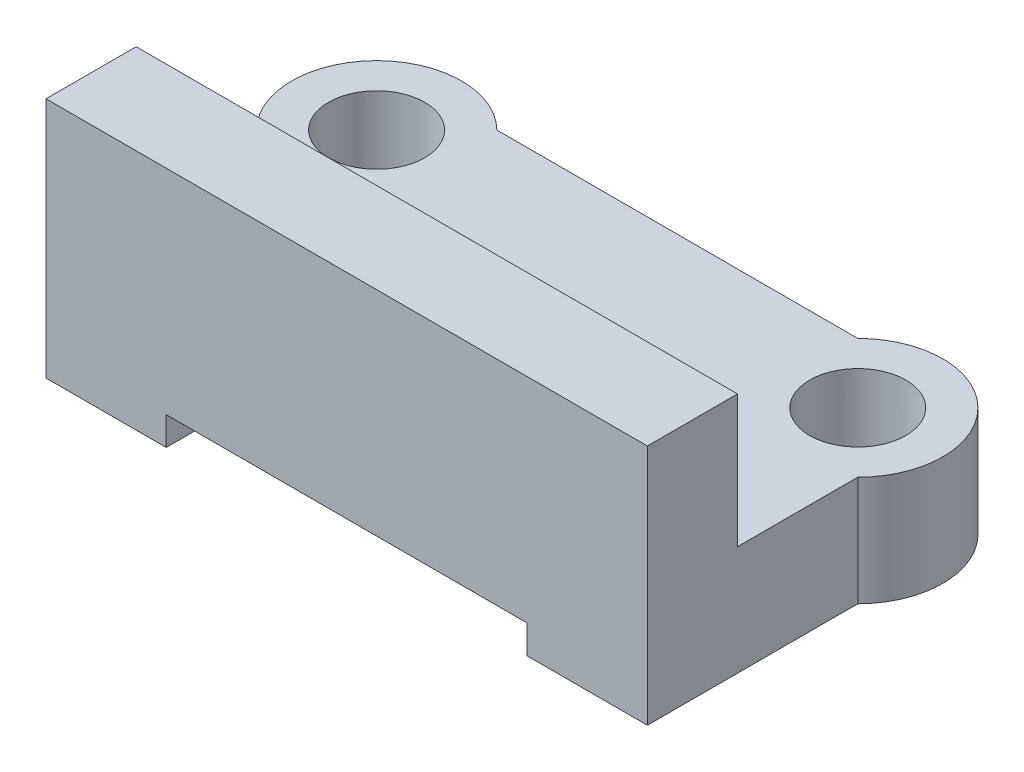
SolidWorks part; units mm, degrees
ref_plane "Front Plane" through (0, 0, 0) normal (0, 0, 1) x (1, 0, 0)
ref_plane "Top Plane" through (0, 0, 0) normal (0, 1, 0) x (1, 0, 0)
ref_plane "Right Plane" through (0, 0, 0) normal (1, 0, 0) x (0, 0, -1)
sketch "Sketch1" plane through (0, 0, 0) normal (0, 0, 1) x (1, 0, 0)
  line L0 (24.6185, -84.9027) -> (24.6185, -85.8498)
  line L1 (36.6261, -85.8498) -> (36.6261, -84.9027)
  line L2 (40.6261, -85.8498) -> (40.6261, -73.2027)
  line L3 (20.6185, -73.2027) -> (20.6185, -85.8498)
  line L6 (36.6261, -84.9027) -> (24.6185, -84.9027)
  line L8 (36.6261, -91.3148) -> (36.6261, -85.5592) construction
  line L10 (20.6185, -85.8498) -> (24.6185, -85.8498)
  line L11 (40.6261, -91.3148) -> (40.6261, -85.5592) construction
  line L14 (20.6185, -85.7535) -> (20.6185, -95.8462) construction
  line L15 (20.6185, -73.2027) -> (40.6261, -73.2027)
  line L16 (24.6185, -85.7535) -> (24.6185, -95.8462) construction
  line L18 (36.6261, -85.8498) -> (40.6261, -85.8498)
  dimension "D2" = 4
extrude "Boss-Extrude1" add sketch "Sketch1" along normal blind 3
sketch "Sketch2" plane through (0, 0, 0) normal (0, 0, -1) x (-1, 0, 0)
  line L0 (-40.6261, -73.2027) -> (-20.6185, -73.2027) construction
  line L1 (-40.6261, -73.2027) -> (-20.6185, -73.2027)
  line L2 (-40.6261, -73.2027) -> (-40.6261, -78.2027)
  line L3 (-40.6261, -78.2027) -> (-20.6185, -78.2027)
  line L4 (-20.6185, -73.2027) -> (-20.6185, -78.2027)
  line L5 (-20.6185, -73.2027) -> (-20.6185, -85.8498) construction
extrude "Boss-Extrude2" add sketch "Sketch2" along normal blind 8
sketch "Sketch3" plane through (0, 0, 0) normal (0, 0, -1) x (-1, 0, 0)
  line L8 (-20.6185, -78.2027) -> (-40.6261, -78.2027)
  line L9 (-40.6261, -78.2027) -> (-40.6261, -85.8498)
  line L10 (-40.6261, -85.8498) -> (-36.6261, -85.8498)
  line L11 (-36.6261, -85.8498) -> (-36.6261, -84.9027)
  line L12 (-36.6261, -84.9027) -> (-24.6185, -84.9027)
  line L13 (-24.6185, -84.9027) -> (-24.6185, -85.8498)
  line L14 (-24.6185, -85.8498) -> (-20.6185, -85.8498)
  line L15 (-20.6185, -85.8498) -> (-20.6185, -78.2027)
  line L17 (-40.6261, -82.2027) -> (-40.6261, -85.8498)
  line L18 (-40.6261, -85.8498) -> (-36.6261, -85.8498)
  line L19 (-36.6261, -85.8498) -> (-36.6261, -84.9027)
  line L20 (-36.6261, -84.9027) -> (-24.6185, -84.9027)
  line L21 (-24.6185, -84.9027) -> (-24.6185, -85.8498)
  line L22 (-24.6185, -85.8498) -> (-20.6185, -85.8498)
  line L23 (-20.6185, -85.8498) -> (-20.6185, -82.2027)
  line L24 (-40.6261, -82.2027) -> (-20.6185, -82.2027)
  dimension "D1" = 0
extrude "Boss-Extrude3" add sketch "Sketch3" along normal blind 8
sketch "Sketch4" plane through (0, 0, 3) normal (0, 0, 1) x (1, 0, 0)
  line L0 (40.6261, -73.2027) -> (20.6185, -73.2027) construction
  line L1 (24.6185, -73.2027) -> (36.6261, -73.2027)
  line L2 (24.6185, -73.2027) -> (24.6185, -74.6027)
  line L3 (24.6185, -74.6027) -> (36.6261, -74.6027)
  line L4 (36.6261, -73.2027) -> (36.6261, -74.6027)
  dimension "D1" = 1.4
extrude "Cut-Extrude1" cut sketch "Sketch4" against normal blind 27.7
hole_wizard "M3 Clearance Hole1" positions "Sketch6" profile "Sketch5" hole size "M3" standard "ISO"
sketch "Sketch6" plane through (0, -73.2027, 0) normal (0, 1, 0) x (1, 0, 0)
  line L0 (20.6185, -3) -> (20.6185, 8) construction
  line L1 (40.6261, -3) -> (40.6261, 8) construction
  line L2 (36.6261, 8) -> (40.6261, 8) construction
  line L3 (20.6185, 8) -> (24.6185, 8) construction
  point P0 (22.6185, 6)
  point P2 (38.6261, 6)
  dimension "D1" = 2
  dimension "D2" = 2
  dimension "D3" = 2
  dimension "D4" = 2
sketch "Sketch5" plane through (22.6185, -73.2027, -6) normal (1, 0, 0) x (0, 0, 1)
  line L0 (0, 0) -> (0, 16.4614)
  line L1 (0, 16.4614) -> (1.6, 15.5)
  line L2 (1.6, 15.5) -> (1.6, 0)
  line L5 (1.6, 0) -> (0, 0)
  line L10 (0, 16.4614) -> (-1.6, 15.5) construction
  line L11 (0, -6.35) -> (0, 107.95) construction
  dimension "Hole Dia." = 3.2
  dimension "Hole Depth" = 15.5
  dimension "Drill Angle" = 118
sketch "Sketch7" plane through (40.6261, 0, 0) normal (1, 0, 0) x (0, 0, -1)
  line L0 (8, -78.2027) -> (0, -78.2027) construction
  line L1 (0, -78.2027) -> (8, -78.2027)
  line L2 (0, -78.2027) -> (0, -77.8027)
  line L3 (0, -77.8027) -> (8, -77.8027)
  line L4 (8, -78.2027) -> (8, -77.8027)
  line L5 (8, -73.2027) -> (8, -78.2027) construction
  dimension "D1" = 0.4
extrude "Cut-Extrude2" cut sketch "Sketch7" against normal blind 28.5
sketch "Sketch8" plane through (0, -73.2027, 0) normal (0, 1, 0) x (1, 0, 0)
  line L0 (20.6185, 4) -> (20.6185, 8)
  line L1 (20.6185, -3) -> (20.6185, 8) construction
  line L2 (20.6185, 8) -> (24.6185, 8)
  line L3 (24.6185, 8) -> (24.6185, -3) construction
  line L4 (40.6261, 8) -> (36.6261, 8)
  line L5 (36.6261, 8) -> (40.6261, 8) construction
  line L8 (40.6261, 8) -> (40.6261, 4)
  line L9 (40.6261, -3) -> (40.6261, 8) construction
  arc A0 (40.6261, 4) -> (36.6261, 8) centre (38.6261, 6) ccw
  arc A1 (24.6185, 8) -> (20.6185, 4) centre (22.6185, 6) ccw
  line M2 (40.6261, 8) -> (36.6261, 8)
  line M5 (40.6261, -3) -> (40.6261, 8)
extrude "Boss-Extrude4" add sketch "Sketch8" against normal up to surface (4.6 mm away) contours L2 A1 | L0 A1 | A0 M2 | A0 M5 up to face at (22.6185, -77.8027, -4.4)
sketch "Sketch9" plane through (0, -85.8498, 0) normal (0, -1, 0) x (1, 0, 0)
  line L0 (20.6185, -4) -> (20.6185, -8)
  line L1 (20.6185, -8) -> (24.6185, -8)
  line L2 (36.6261, -8) -> (40.6261, -8)
  line L3 (40.6261, -8) -> (40.6261, -4)
  arc A0 (20.6185, -4) -> (24.6185, -8) centre (22.6185, -6) ccw construction
  arc A1 (20.6185, -4) -> (24.6185, -8) centre (22.6185, -6) ccw
  arc A2 (36.6261, -8) -> (40.6261, -4) centre (38.6261, -6) ccw construction
  arc A3 (36.6261, -8) -> (40.6261, -4) centre (38.6261, -6) ccw
  line M2 (20.6185, 3) -> (20.6185, -8)
  line M3 (20.6185, -8) -> (24.6185, -8)
extrude "Boss-Extrude5" add sketch "Sketch9" against normal up to surface (3.6471 mm away) contours A1 M2 | A1 M3 | L2 A3 | L3 A3 up to face at (22.6185, -82.2027, -7.6)
sketch "Sketch10" plane through (0, 0, 3) normal (0, 0, 1) x (1, 0, 0)
  line L1 (17.0109, -70.1968) -> (42.7707, -70.1968)
  line L2 (17.0109, -70.1968) -> (17.0109, -77.8027)
  line L3 (17.0109, -77.8027) -> (42.7707, -77.8027)
  line L4 (42.7707, -70.1968) -> (42.7707, -77.8027)
extrude "Cut-Extrude3" cut sketch "Sketch10" against normal blind 15
